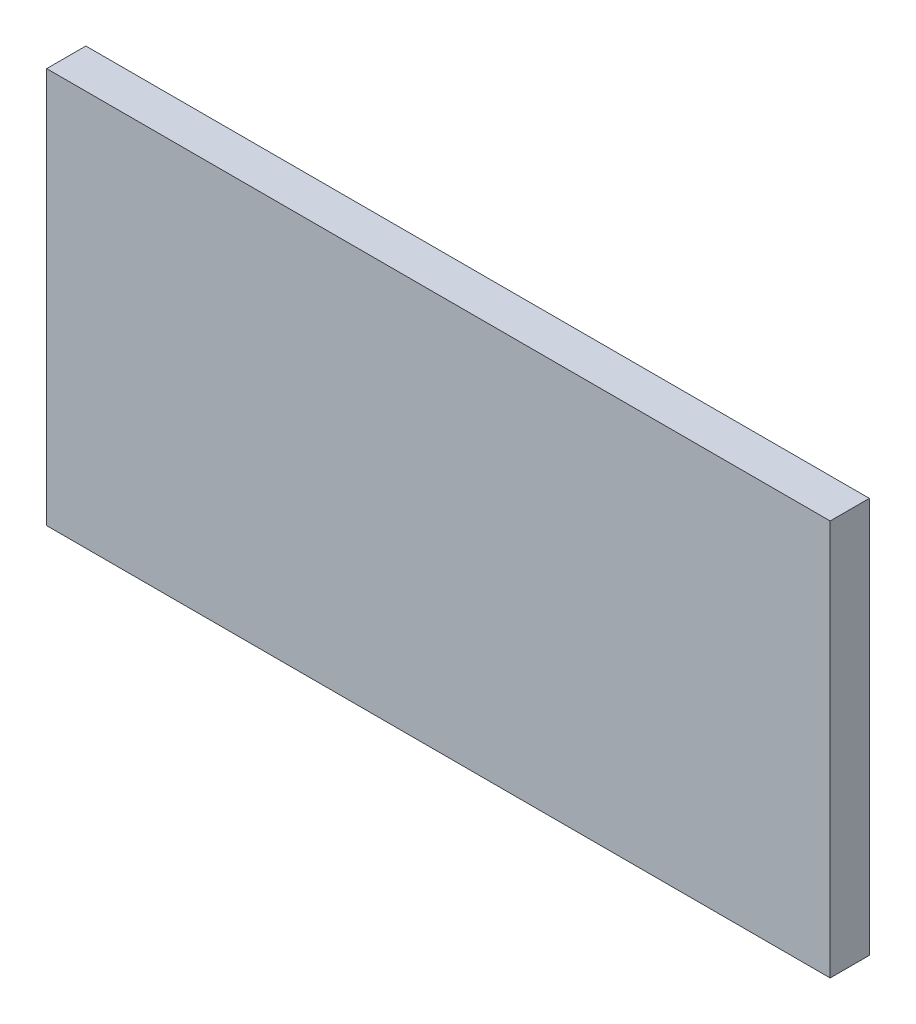
SolidWorks part; units mm, degrees
ref_plane "Front Plane" through (0, 0, 0) normal (0, 0, 1) x (1, 0, 0)
ref_plane "Top Plane" through (0, 0, 0) normal (0, 1, 0) x (1, 0, 0)
ref_plane "Right Plane" through (0, 0, 0) normal (1, 0, 0) x (0, 0, -1)
sketch "Sketch1" plane through (0, 0, 0) normal (1, 0, 0) x (0, 0, -1)
  line L22 (0, 0) -> (12, 0)
  line L23 (0, 0) -> (0, -121.24)
  line L24 (0, -121.24) -> (12, -121.24)
  line L25 (12, 0) -> (12, -121.24)
extrude "Boss-Extrude1" add sketch "Sketch1" against normal blind 240
